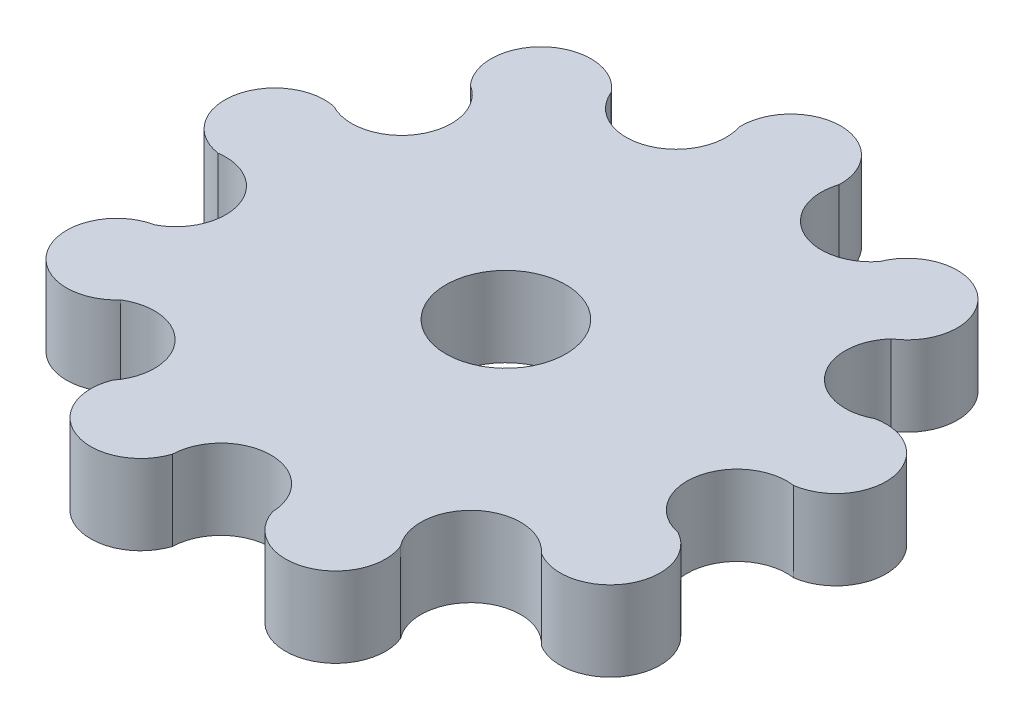
SolidWorks part; units mm, degrees
material "1060 Alloy"
ref_plane "Front" through (0, 0, 0) normal (0, 0, 1) x (1, 0, 0)
ref_plane "Top" through (0, 0, 0) normal (0, 1, 0) x (1, 0, 0)
ref_plane "Right" through (0, 0, 0) normal (1, 0, 0) x (0, 0, -1)
sketch "Sketch1" plane through (0, 0, 0) normal (0, 1, 0) x (1, 0, 0)
  line L1 (-55, 0) -> (55, 0) construction
  circle A0 centre (0, 0) radius 28.5
  circle A1 centre (0, 28.5) radius 5
  circle A16 centre (9.7476, 26.7812) radius 5
  circle A17 centre (18.3194, 21.8323) radius 5
  circle A18 centre (24.6817, 14.25) radius 5
  circle A19 centre (28.067, 4.949) radius 5
  circle A20 centre (28.067, -4.949) radius 5
  circle A21 centre (24.6817, -14.25) radius 5
  circle A22 centre (18.3194, -21.8323) radius 5
  circle A23 centre (9.7476, -26.7812) radius 5
  circle A24 centre (0, -28.5) radius 5
  circle A25 centre (-9.7476, -26.7812) radius 5
  circle A26 centre (-18.3194, -21.8323) radius 5
  circle A27 centre (-24.6817, -14.25) radius 5
  circle A28 centre (-28.067, -4.949) radius 5
  circle A29 centre (-28.067, 4.949) radius 5
  circle A30 centre (-24.6817, 14.25) radius 5
  circle A31 centre (-18.3194, 21.8323) radius 5
  circle A32 centre (-9.7476, 26.7812) radius 5
  point P36 (-1.5003, 0)
  point P45 (0, 0)
  dimension "D1" = 57
  dimension "D2" = 10
  dimension "D3" = 18
extrude "Boss-Extrude2" add sketch "Sketch1" along normal blind 8 contours A32 A0 A31 A30 A29 A28 A27 A26 A25 A24 A23 A22 A21 A20 A19 A18 A17 A16 A1 | A0 A1 | A0 A1 | A0 A17 | A0 A17 | A0 A19 | A0 A19 | A0 A21 | A0 A21 | A0 A23 | A0 A23 | A0 A25 | A0 A25 | A0 A27 | A0 A27 | A0 A29 | A0 A29 | A0 A31 | A0 A31
sketch "Sketch2" plane through (0, 8, 0) normal (0, 1, 0) x (1, 0, 0)
  circle A0 centre (0, 0) radius 6
  dimension "D1" = 12
extrude "Cut-Extrude1" cut sketch "Sketch2" against normal blind 10
